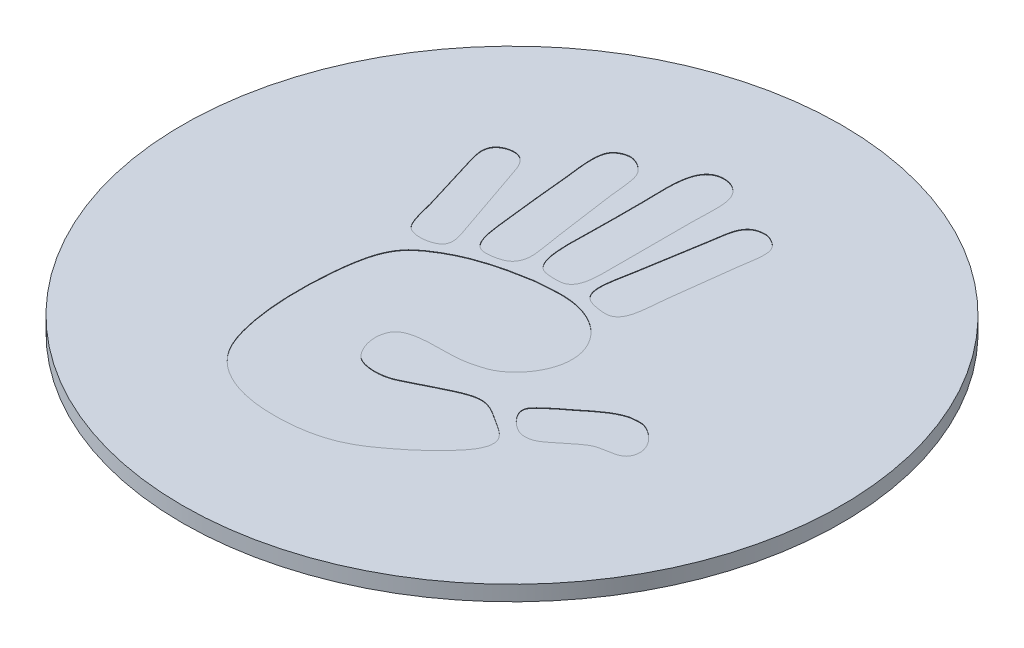
SolidWorks part; units mm, degrees
ref_plane "Front Plane" through (0, 0, 0) normal (0, 0, 1) x (1, 0, 0)
ref_plane "Top Plane" through (0, 0, 0) normal (0, 1, 0) x (1, 0, 0)
ref_plane "Right Plane" through (0, 0, 0) normal (1, 0, 0) x (0, 0, -1)
sketch "Sketch2" plane through (0, 0, 0) normal (0, 1, 0) x (1, 0, 0)
  line L0 (-23.6354, -2.1803) -> (-14.8134, -18.5314)
  line L1 (-14.8134, -18.5314) -> (-14.0145, -18.1003)
  line L2 (22.4832, 1.5913) -> (23.6354, 2.213)
  line L3 (23.6354, 2.213) -> (14.8311, 18.5314)
  line L4 (14.8311, 18.5314) -> (13.9151, 18.0372)
  arc A0 (-9.0807, -18.0316) -> (-14.0145, -18.1003) centre (-11.4817, -22.7946) ccw
  arc A1 (-9.0807, -18.0316) -> (20.1042, -1.9833) centre (0.0088, 0) ccw
  arc A2 (22.4832, 1.5913) -> (20.1042, -1.9833) centre (24.6541, -2.4324) ccw
  arc A3 (9.1926, 17.9838) -> (13.9151, 18.0372) centre (11.503, 22.508) ccw
  arc A4 (9.1926, 17.9838) -> (-20.1066, 1.7689) centre (0.0088, 0) ccw
  ellipse E0 centre (-32.3362, 6.0706) end of major axis (8.5219, 28.1148) minor radius 11.43 (-23.6354, -2.1803) -> (-22.0132, -1.2522) ccw
  spline S0 degree 3 poles (-20.1066, 1.7689) (-20.1338, 1.4588) (-20.1972, 1.1538) (-20.3941, 0.5658) (-20.5253, 0.2882) (-20.7711, -0.1034) (-20.8619, -0.2306) (-21.057, -0.4712) (-21.1612, -0.585) (-21.4939, -0.9069) (-21.7437, -1.0962) (-22.0132, -1.2522) knots 0 0 0 0 0.25 0.25 0.5 0.5 0.625 0.625 0.75 0.75 1 1 1 1
extrude "Boss-Extrude1" add sketch "Sketch2" along normal blind 0.762
sketch "Sketch3" plane through (0, 0.762, 0) normal (0, 1, 0) x (1, 0, 0)
  spline S0 degree 3 poles (-1.1282, 2.7342) (-1.8691, 3.0923) (-1.6328, 5.0692) (-1.6328, 6.1571) (-1.6328, 6.9066) (-1.6328, 7.5655) (-1.6328, 8.1319) (-1.6328, 9.3443) (-1.8554, 11.0728) (-0.7552, 11.2257) knots 5 5 5 5 6 6 6 7 7 7 8 8 8 8
  spline S1 degree 3 poles (-0.053, 2.6903) (-0.229, 2.6221) (-0.8719, 2.6103) (-1.1282, 2.7342) knots 4 4 4 4 5 5 5 5
  spline S2 degree 3 poles (0.4077, 10.5016) (0.5656, 10.0125) (0.4736, 9.223) (0.4736, 8.461) (0.4736, 7.07) (0.4736, 5.6932) (0.4736, 4.2482) (0.4736, 3.4538) (0.3961, 2.8645) (-0.053, 2.6903) knots 1 1 1 1 2 2 2 3 3 3 4 4 4 4
  spline S3 degree 3 poles (-0.7552, 11.2257) (-0.2196, 11.3) (0.2501, 10.99) (0.4077, 10.5016) knots 0 0 0 0 1 1 1 1
  spline S4 degree 3 poles (1.7462, 8.2196) (1.8785, 9.0626) (1.8991, 9.833) (2.7994, 9.8653) knots 7 7 7 7 8 8 8 8
  spline S5 degree 3 poles (1.1977, 4.9064) (1.3429, 5.8845) (1.5932, 7.2455) (1.7462, 8.2196) knots 6 6 6 6 7 7 7 7
  spline S6 degree 3 poles (1.3074, 2.6245) (0.7186, 3.0259) (1.0791, 4.1085) (1.1977, 4.9064) knots 5 5 5 5 6 6 6 6
  spline S7 degree 3 poles (2.4703, 2.427) (2.2313, 2.3604) (1.567, 2.4475) (1.3074, 2.6245) knots 4 4 4 4 5 5 5 5
  spline S8 degree 3 poles (3.1724, 4.5553) (3.0722, 3.7942) (3.1347, 2.6121) (2.4703, 2.427) knots 3 3 3 3 4 4 4 4
  spline S9 degree 3 poles (3.5674, 7.715) (3.441, 6.6447) (3.3126, 5.6204) (3.1724, 4.5553) knots 2 2 2 2 3 3 3 3
  spline S10 degree 3 poles (3.6551, 9.3167) (3.8064, 8.9128) (3.6305, 8.2498) (3.5674, 7.715) knots 1 1 1 1 2 2 2 2
  spline S11 degree 3 poles (2.7994, 9.8653) (3.0754, 9.8752) (3.5326, 9.6439) (3.6551, 9.3167) knots 0 0 0 0 1 1 1 1
  spline S12 degree 3 poles (-4.6169, 9.4703) (-4.4887, 9.681) (-4.2271, 9.8127) (-3.9806, 9.8433) knots 9 9 9 9 10 10 10 10
  spline S13 degree 3 poles (-4.6389, 7.4078) (-4.6837, 7.8997) (-4.9009, 9.0037) (-4.6169, 9.4703) knots 8 8 8 8 9 9 9 9
  spline S14 degree 3 poles (-4.222, 3.5241) (-4.3769, 4.8172) (-4.5206, 6.1106) (-4.6389, 7.4078) knots 7 7 7 7 8 8 8 8
  spline S15 degree 3 poles (-3.5198, 2.054) (-3.9874, 2.1488) (-4.1348, 2.7966) (-4.222, 3.5241) knots 6 6 6 6 7 7 7 7
  spline S16 degree 3 poles (-2.4447, 2.2514) (-2.6908, 2.0945) (-3.2317, 1.9955) (-3.5198, 2.054) knots 5 5 5 5 6 6 6 6
  spline S17 degree 3 poles (-2.0717, 3.2608) (-2.0334, 2.7464) (-2.1681, 2.4279) (-2.4447, 2.2514) knots 4 4 4 4 5 5 5 5
  spline S18 degree 3 poles (-2.2911, 4.7089) (-2.2318, 4.2203) (-2.1058, 3.7197) (-2.0717, 3.2608) knots 3 3 3 3 4 4 4 4
  spline S19 degree 3 poles (-2.708, 7.6711) (-2.5762, 6.7374) (-2.4088, 5.6781) (-2.2911, 4.7089) knots 2 2 2 2 3 3 3 3
  spline S20 degree 3 poles (-2.9274, 9.1412) (-2.7836, 8.7431) (-2.7721, 8.1254) (-2.708, 7.6711) knots 1 1 1 1 2 2 2 2
  spline S21 degree 3 poles (-3.9806, 9.8433) (-3.604, 9.8902) (-3.0714, 9.5397) (-2.9274, 9.1412) knots 0 0 0 0 1 1 1 1
  spline S22 degree 3 poles (-7.8424, 6.6618) (-7.7338, 6.9558) (-7.4296, 7.1155) (-7.1183, 7.1445) knots 7 7 7 7 8 8 8 8
  spline S23 degree 3 poles (-7.6449, 5.3233) (-7.7743, 5.7642) (-7.9833, 6.2802) (-7.8424, 6.6618) knots 6 6 6 6 7 7 7 7
  spline S24 degree 3 poles (-6.8769, 2.8) (-7.1115, 3.6067) (-7.3842, 4.4353) (-7.6449, 5.3233) knots 5 5 5 5 6 6 6 6
  spline S25 degree 3 poles (-6.2845, 1.2421) (-6.6209, 1.5236) (-6.7319, 2.3011) (-6.8769, 2.8) knots 4 4 4 4 5 5 5 5
  spline S26 degree 3 poles (-4.7486, 1.4396) (-4.9781, 1.051) (-5.9312, 0.9465) (-6.2845, 1.2421) knots 3 3 3 3 4 4 4 4
  spline S27 degree 3 poles (-4.7925, 2.2734) (-4.6988, 2.0073) (-4.6208, 1.656) (-4.7486, 1.4396) knots 2 2 2 2 3 3 3 3
  spline S28 degree 3 poles (-6.0212, 5.8499) (-5.5882, 4.5893) (-5.2231, 3.4967) (-4.7925, 2.2734) knots 1 1 1 1 2 2 2 2
  spline S29 degree 3 poles (-7.1183, 7.1445) (-6.3685, 7.2142) (-6.2026, 6.378) (-6.0212, 5.8499) knots 0 0 0 0 1 1 1 1
  spline S30 degree 3 poles (-0.9526, 2.054) (-0.6589, 2.1008) (-0.3704, 2.0916) (-0.053, 2.1198) knots 19 19 19 19 20 20 20 20
  spline S31 degree 3 poles (-4.4853, 0.9349) (-3.4767, 1.523) (-2.3419, 1.8327) (-0.9526, 2.054) knots 18 18 18 18 19 19 19 19
  spline S32 degree 3 poles (-5.5385, 0.1231) (-5.2793, 0.4341) (-4.8654, 0.7133) (-4.4853, 0.9349) knots 17 17 17 17 18 18 18 18
  spline S33 degree 3 poles (-6.3503, -2.5977) (-6.2452, -1.4933) (-6.0872, -0.5353) (-5.5385, 0.1231) knots 16 16 16 16 17 17 17 17
  spline S34 degree 3 poles (-5.736, -8.2806) (-6.3878, -6.9135) (-6.5412, -4.6031) (-6.3503, -2.5977) knots 15 15 15 15 16 16 16 16
  spline S35 degree 3 poles (-3.2565, -10.1237) (-4.3956, -9.8398) (-5.2824, -9.2318) (-5.736, -8.2806) knots 14 14 14 14 15 15 15 15
  spline S36 degree 3 poles (0.6052, -10.014) (-0.609, -10.3752) (-2.1621, -10.3965) (-3.2565, -10.1237) knots 13 13 13 13 14 14 14 14
  spline S37 degree 3 poles (3.3041, -8.3903) (2.4642, -9.0707) (1.7022, -9.6877) (0.6052, -10.014) knots 12 12 12 12 13 13 13 13
  spline S38 degree 3 poles (4.4012, -7.3371) (4.0062, -7.7674) (3.6976, -8.0715) (3.3041, -8.3903) knots 11 11 11 11 12 12 12 12
  spline S39 degree 3 poles (5.1033, -5.9109) (5.1971, -6.4361) (4.6917, -7.0206) (4.4012, -7.3371) knots 10 10 10 10 11 11 11 11
  spline S40 degree 3 poles (4.2037, -5.0113) (4.5637, -5.2444) (5.0302, -5.5017) (5.1033, -5.9109) knots 9 9 9 9 10 10 10 10
  spline S41 degree 3 poles (2.9749, -4.4408) (3.4311, -4.4667) (3.8131, -4.7584) (4.2037, -5.0113) knots 8 8 8 8 9 9 9 9
  spline S42 degree 3 poles (1.2415, -5.0332) (1.7438, -4.8021) (2.426, -4.4096) (2.9749, -4.4408) knots 7 7 7 7 8 8 8 8
  spline S43 degree 3 poles (-0.3383, -5.7792) (0.0666, -5.6579) (0.6458, -5.3074) (1.2415, -5.0332) knots 6 6 6 6 7 7 7 7
  spline S44 degree 3 poles (-1.8303, -5.6915) (-1.4448, -5.9058) (-0.813, -5.9215) (-0.3383, -5.7792) knots 5 5 5 5 6 6 6 6
  spline S45 degree 3 poles (-2.3569, -3.8923) (-2.639, -4.5973) (-2.222, -5.4737) (-1.8303, -5.6915) knots 4 4 4 4 5 5 5 5
  spline S46 degree 3 poles (1.0221, -3.1462) (-0.0727, -3.4118) (-1.9845, -2.9614) (-2.3569, -3.8923) knots 3 3 3 3 4 4 4 4
  spline S47 degree 3 poles (1.9217, -2.861) (1.668, -2.9888) (1.3595, -3.0644) (1.0221, -3.1462) knots 2 2 2 2 3 3 3 3
  spline S48 degree 3 poles (3.2602, 0.4522) (3.8474, -0.9459) (2.8718, -2.3826) (1.9217, -2.861) knots 1 1 1 1 2 2 2 2
  spline S49 degree 3 poles (-0.053, 2.1198) (1.5494, 2.2621) (2.8008, 1.546) (3.2602, 0.4522) knots 0 0 0 0 1 1 1 1
  spline S50 degree 3 poles (7.3633, -1.4787) (7.4269, -1.4613) (7.4808, -1.4669) (7.5608, -1.4567) knots 9 9 9 9 10 10 10 10
  spline S51 degree 3 poles (5.7177, -2.5099) (6.2197, -2.0983) (6.741, -1.6482) (7.3633, -1.4787) knots 8 8 8 8 9 9 9 9
  spline S52 degree 3 poles (4.9716, -3.1023) (5.217, -2.8771) (5.5051, -2.6842) (5.7177, -2.5099) knots 7 7 7 7 8 8 8 8
  spline S53 degree 3 poles (4.3792, -3.8484) (4.3841, -3.5626) (4.6846, -3.3658) (4.9716, -3.1023) knots 6 6 6 6 7 7 7 7
  spline S54 degree 3 poles (5.3885, -4.9235) (4.9957, -4.8403) (4.3719, -4.2718) (4.3792, -3.8484) knots 5 5 5 5 6 6 6 6
  spline S55 degree 3 poles (6.7709, -4.3311) (6.3624, -4.6332) (6.0227, -5.0578) (5.3885, -4.9235) knots 4 4 4 4 5 5 5 5
  spline S56 degree 3 poles (7.7144, -3.6509) (7.3893, -3.7984) (7.0606, -4.1168) (6.7709, -4.3311) knots 3 3 3 3 4 4 4 4
  spline S57 degree 3 poles (9.0748, -3.1462) (8.8596, -3.5448) (8.1193, -3.4671) (7.7144, -3.6509) knots 2 2 2 2 3 3 3 3
  spline S58 degree 3 poles (8.0435, -1.4567) (8.5718, -1.5848) (9.4765, -2.402) (9.0748, -3.1462) knots 1 1 1 1 2 2 2 2
  spline S59 degree 3 poles (7.5608, -1.4567) (7.6413, -1.4465) (7.861, -1.4124) (8.0435, -1.4567) knots 0 0 0 0 1 1 1 1
extrude "Cut-Extrude1" cut sketch "Sketch3" against normal through all
sketch "Sketch5" plane through (0, 0.762, 0) normal (0, 1, 0) x (1, 0, 0)
  line L1 (-29.848, 33.7391) -> (37.109, 33.7391)
  line L2 (-29.848, 33.7391) -> (-29.848, -32.9665)
  line L3 (-29.848, -32.9665) -> (37.109, -32.9665)
  line L4 (37.109, 33.7391) -> (37.109, -32.9665)
  circle A0 centre (0.0088, 0) radius 20.193 construction
  circle A1 centre (0.0088, 0) radius 16.51
  dimension "D1" = 33.02
extrude "Cut-Extrude2" cut sketch "Sketch5" against normal through all
sketch "Sketch7" plane through (0, 0.762, 0) normal (0, 1, 0) x (1, 0, 0)
  circle A2 centre (0.0088, 0) radius 16.51
  circle A3 centre (0.0088, 0) radius 16.51
  dimension "D1" = 0
extrude "Boss-Extrude3" add sketch "Sketch7" against normal offset from surface (0.7366 mm away) 0.0254 up to face at (-0.3822, 0, -6.7879)
sketch "Sketch9" plane through (0, 0.762, 0) normal (0, 1, 0) x (1, 0, 0)
  spline S16 degree 3 poles (-3095.764, -2526.2399) (3123.3369, 2562.8139) (-3137.3899, -2533.6941) (3146.6231, 2473.272) knots -8.557527 -8.557527 -8.557527 -8.557527 19.035336 19.035336 19.035336 19.035336 only from (1.1977, 4.9064) to (1.3074, 2.6245)
  spline S17 degree 3 poles (-1016.7765, -3859.7939) (1035.8712, 3952.7013) (-1035.3417, -3938.9025) (1026.935, 3870.8828) knots -10.71349 -10.71349 -10.71349 -10.71349 23.715667 23.715667 23.715667 23.715667 only from (1.7462, 8.2196) to (1.1977, 4.9064)
  spline S18 degree 3 poles (3295.5782, -2260.9631) (-3314.7192, 2281.6665) (3348.36, -2219.0011) (-3382.3927, 2139.6319) knots -7.025242 -7.025242 -7.025242 -7.025242 22.935092 22.935092 22.935092 22.935092 only from (2.7994, 9.8653) to (1.7462, 8.2196)
  spline S19 degree 3 poles (-3898.3126, 884.962) (3893.2425, -1014.2368) (-3849.031, 1168.6789) (3791.5327, -1270.3118) knots -19.012311 -19.012311 -19.012311 -19.012311 20.118792 20.118792 20.118792 20.118792 only from (3.6551, 9.3167) to (2.7994, 9.8653)
  spline S20 degree 3 poles (3003.7237, 2652.8791) (-3013.6529, -2668.401) (3031.1782, 2672.8873) (-3027.1825, -2600.7338) knots -17.720569 -17.720569 -17.720569 -17.720569 20.297542 20.297542 20.297542 20.297542 only from (3.5674, 7.715) to (3.6551, 9.3167)
  spline S21 degree 3 poles (-471.1883, -3966.9869) (441.5568, 3832.8889) (-417.0462, -3822.7841) (424.5912, 3985.2122) knots -32.960104 -32.960104 -32.960104 -32.960104 37.918216 37.918216 37.918216 37.918216 only from (3.1724, 4.5553) to (3.5674, 7.715)
  spline S22 degree 3 poles (-2179.0397, 3354.8429) (2155.2022, -3411.1409) (-2123.0133, 3435.5851) (2107.3587, -3397.0534) knots -9.664312 -9.664312 -9.664312 -9.664312 17.136069 17.136069 17.136069 17.136069 only from (2.4703, 2.427) to (3.1724, 4.5553)
  spline S23 degree 3 poles (3995.8195, -198.2506) (-4017.7675, 277.0857) (4016.2829, -340.9695) (-3976.4498, 409.4185) knots -12.428208 -12.428208 -12.428208 -12.428208 21.381402 21.381402 21.381402 21.381402 only from (1.3074, 2.6245) to (2.4703, 2.427)
  spline S24 degree 3 poles (1.1977, 4.9064) (1.0791, 4.1085) (0.7186, 3.0259) (1.3074, 2.6245) knots 5 5 5 5 6 6 6 6
  spline S25 degree 3 poles (1.7462, 8.2196) (1.5932, 7.2455) (1.3429, 5.8845) (1.1977, 4.9064) knots 6 6 6 6 7 7 7 7
  spline S26 degree 3 poles (2.7994, 9.8653) (1.8991, 9.833) (1.8785, 9.0626) (1.7462, 8.2196) knots 7 7 7 7 8 8 8 8
  spline S27 degree 3 poles (3.6551, 9.3167) (3.5326, 9.6439) (3.0754, 9.8752) (2.7994, 9.8653) knots 0 0 0 0 1 1 1 1
  spline S28 degree 3 poles (3.5674, 7.715) (3.6305, 8.2498) (3.8064, 8.9128) (3.6551, 9.3167) knots 1 1 1 1 2 2 2 2
  spline S29 degree 3 poles (3.1724, 4.5553) (3.3126, 5.6204) (3.441, 6.6447) (3.5674, 7.715) knots 2 2 2 2 3 3 3 3
  spline S30 degree 3 poles (2.4703, 2.427) (3.1347, 2.6121) (3.0722, 3.7942) (3.1724, 4.5553) knots 3 3 3 3 4 4 4 4
  spline S31 degree 3 poles (1.3074, 2.6245) (1.567, 2.4475) (2.2313, 2.3604) (2.4703, 2.427) knots 4 4 4 4 5 5 5 5
  spline S32 degree 3 poles (-3175.8378, 2434.3295) (-36.4904, 67.3954) (0.4736, -13.1033) (0.4736, 4.2482) (0.4736, 5.6932) (0.4736, 7.07) (0.4736, 8.461) (0.4736, 24.1547) (39.5081, 51.547) (-2869.5101, -2775.5992) knots -19.842069 -19.842069 -19.842069 -19.842069 2 2 2 3 3 3 23.596173 23.596173 23.596173 23.596173 only from (-0.053, 2.6903) to (0.4077, 10.5016)
  spline S33 degree 3 poles (3972.5737, 458.22) (-4007.8398, -396.4799) (4011.7989, 346.3165) (-3989.3096, -286.5983) knots -12.275486 -12.275486 -12.275486 -12.275486 21.202959 21.202959 21.202959 21.202959 only from (-1.1282, 2.7342) to (-0.053, 2.6903)
  spline S34 degree 3 poles (2436.5507, -3160.0671) (-32.5536, 108.4317) (-1.6328, 22.4233) (-1.6328, 8.1319) (-1.6328, 7.5655) (-1.6328, 6.9066) (-1.6328, 6.1571) (-1.6328, -6.5094) (-33.6617, -139.6907) (1817.5783, 3564.7777) knots -5.787592 -5.787592 -5.787592 -5.787592 6 6 6 7 7 7 18.643178 18.643178 18.643178 18.643178 only from (-0.7552, 11.2257) to (-1.1282, 2.7342)
  spline S35 degree 3 poles (-3382.9717, 2135.2595) (3184.6086, -2420.1101) (-2952.2242, 2719.3511) (2686.5942, -2945.1574) knots -22.773491 -22.773491 -22.773491 -22.773491 23.550804 23.550804 23.550804 23.550804 only from (0.4077, 10.5016) to (-0.7552, 11.2257)
  spline S36 degree 3 poles (-0.053, 2.6903) (0.3961, 2.8645) (0.4736, 3.4538) (0.4736, 4.2482) (0.4736, 5.6932) (0.4736, 7.07) (0.4736, 8.461) (0.4736, 9.223) (0.5656, 10.0125) (0.4077, 10.5016) knots 1 1 1 1 2 2 2 3 3 3 4 4 4 4
  spline S37 degree 3 poles (-1.1282, 2.7342) (-0.8719, 2.6103) (-0.229, 2.6221) (-0.053, 2.6903) knots 4 4 4 4 5 5 5 5
  spline S38 degree 3 poles (-0.7552, 11.2257) (-1.8554, 11.0728) (-1.6328, 9.3443) (-1.6328, 8.1319) (-1.6328, 7.5655) (-1.6328, 6.9066) (-1.6328, 6.1571) (-1.6328, 5.0692) (-1.8691, 3.0923) (-1.1282, 2.7342) knots 5 5 5 5 6 6 6 7 7 7 8 8 8 8
  spline S39 degree 3 poles (0.4077, 10.5016) (0.2501, 10.99) (-0.2196, 11.3) (-0.7552, 11.2257) knots 0 0 0 0 1 1 1 1
  spline S56 degree 3 poles (3827.6525, 1135.0392) (-3871.1576, -816.4124) (3856.8167, 835.4945) (-3815.5815, -1186.8377) knots -55.966256 -55.966256 -55.966256 -55.966256 73.431662 73.431662 73.431662 73.431662 only from (-4.6389, 7.4078) to (-4.222, 3.5241)
  spline S57 degree 3 poles (1977.2357, -3464.7223) (-1941.6752, 3552.5708) (1883.3645, -3562.5842) (-1840.2246, 3561.15) knots -5.595375 -5.595375 -5.595375 -5.595375 22.721906 22.721906 22.721906 22.721906 only from (-4.6169, 9.4703) to (-4.6389, 7.4078)
  spline S58 degree 3 poles (-3913.3808, -831.1765) (3959.9311, 686.2838) (-3993.4882, -493.8088) (3981.036, 332.26) knots -20.702281 -20.702281 -20.702281 -20.702281 39.096568 39.096568 39.096568 39.096568 only from (-3.9806, 9.8433) to (-4.6169, 9.4703)
  spline S59 degree 3 poles (-3499.6444, 1949.2057) (3430.2664, -2092.6878) (-3345.6841, 2254.2554) (3219.2873, -2356.8577) knots -17.912337 -17.912337 -17.912337 -17.912337 18.843591 18.843591 18.843591 18.843591 only from (-2.9274, 9.1412) to (-3.9806, 9.8433)
  spline S60 degree 3 poles (1724.1373, 3615.5728) (-1744.3122, -3633.9872) (1757.7666, 3641.1516) (-1786.6717, -3570.9141) knots -19.760193 -19.760193 -19.760193 -19.760193 22.558671 22.558671 22.558671 22.558671 only from (-2.708, 7.6711) to (-2.9274, 9.1412)
  spline S61 degree 3 poles (-1516.3629, 3706.7271) (1510.0822, -3805.8224) (-1498.6079, 3824.3616) (1462.195, -3714.1649) knots -23.546646 -23.546646 -23.546646 -23.546646 28.426834 28.426834 28.426834 28.426834 only from (-2.2911, 4.7089) to (-2.708, 7.6711)
  spline S62 degree 3 poles (-3796.6164, 1267.9633) (3807.4648, -1300.3085) (-3817.0278, 1292.6119) (3807.7226, -1211.921) knots -25.260779 -25.260779 -25.260779 -25.260779 32.459145 32.459145 32.459145 32.459145 only from (-2.0717, 3.2608) to (-2.2911, 4.7089)
  spline S63 degree 3 poles (1684.9837, -3620.1859) (-1989.6705, 3573.8882) (2122.2532, -3484.8728) (-2148.6775, 3378.0896) knots -39.439829 -39.439829 -39.439829 -39.439829 41.201324 41.201324 41.201324 41.201324 only from (-2.4447, 2.2514) to (-2.0717, 3.2608)
  spline S64 degree 3 poles (3907.7355, 837.7287) (-3959.5817, -758.6069) (3968.3, 682.0826) (-3957.6475, -591.5849) knots -13.834269 -13.834269 -13.834269 -13.834269 24.829077 24.829077 24.829077 24.829077 only from (-3.5198, 2.054) to (-2.4447, 2.2514)
  spline S65 degree 3 poles (-1936.2727, -3498.7736) (1931.3677, 3558.6844) (-1949.2937, -3544.9252) (1955.9246, 3488.9566) knots -13.737129 -13.737129 -13.737129 -13.737129 25.367565 25.367565 25.367565 25.367565 only from (-4.222, 3.5241) to (-3.5198, 2.054)
  spline S66 degree 3 poles (-4.6389, 7.4078) (-4.5206, 6.1106) (-4.3769, 4.8172) (-4.222, 3.5241) knots 7 7 7 7 8 8 8 8
  spline S67 degree 3 poles (-4.6169, 9.4703) (-4.9009, 9.0037) (-4.6837, 7.8997) (-4.6389, 7.4078) knots 8 8 8 8 9 9 9 9
  spline S68 degree 3 poles (-3.9806, 9.8433) (-4.2271, 9.8127) (-4.4887, 9.681) (-4.6169, 9.4703) knots 9 9 9 9 10 10 10 10
  spline S69 degree 3 poles (-2.9274, 9.1412) (-3.0714, 9.5397) (-3.604, 9.8902) (-3.9806, 9.8433) knots 0 0 0 0 1 1 1 1
  spline S70 degree 3 poles (-2.708, 7.6711) (-2.7721, 8.1254) (-2.7836, 8.7431) (-2.9274, 9.1412) knots 1 1 1 1 2 2 2 2
  spline S71 degree 3 poles (-2.2911, 4.7089) (-2.4088, 5.6781) (-2.5762, 6.7374) (-2.708, 7.6711) knots 2 2 2 2 3 3 3 3
  spline S72 degree 3 poles (-2.0717, 3.2608) (-2.1058, 3.7197) (-2.2318, 4.2203) (-2.2911, 4.7089) knots 3 3 3 3 4 4 4 4
  spline S73 degree 3 poles (-2.4447, 2.2514) (-2.1681, 2.4279) (-2.0334, 2.7464) (-2.0717, 3.2608) knots 4 4 4 4 5 5 5 5
  spline S74 degree 3 poles (-3.5198, 2.054) (-3.2317, 1.9955) (-2.6908, 2.0945) (-2.4447, 2.2514) knots 5 5 5 5 6 6 6 6
  spline S75 degree 3 poles (-4.222, 3.5241) (-4.1348, 2.7966) (-3.9874, 2.1488) (-3.5198, 2.054) knots 6 6 6 6 7 7 7 7
  spline S82 degree 3 poles (3013.787, 2622.1984) (-3147.5515, -2384.3751) (3213.061, 2291.0263) (-3266.8481, -2314.6818) knots -34.0885 -34.0885 -34.0885 -34.0885 45.568972 45.568972 45.568972 45.568972 only from (-7.6449, 5.3233) to (-6.8769, 2.8)
  spline S83 degree 3 poles (3612.8173, -1692.9166) (-3628.3953, 1766.2394) (3601.3377, -1779.3604) (-3593.5352, 1777.2391) knots -13.555681 -13.555681 -13.555681 -13.555681 27.120073 27.120073 27.120073 27.120073 only from (-7.8424, 6.6618) to (-7.6449, 5.3233)
  spline S84 degree 3 poles (-3999.2381, -217.3164) (4015.5257, 32.7299) (-4025.5663, 182.1603) (3972.7996, -370.171) knots -20.762782 -20.762782 -20.762782 -20.762782 34.659546 34.659546 34.659546 34.659546 only from (-7.1183, 7.1445) to (-7.8424, 6.6618)
  spline S85 degree 3 poles (1714.1461, 3616.8704) (-1760.0638, -3616.4555) (1792.9824, 3606.1701) (-1862.0065, -3536.3391) knots -14.162413 -14.162413 -14.162413 -14.162413 14.57936 14.57936 14.57936 14.57936 only from (-6.0212, 5.8499) to (-7.1183, 7.1445)
  spline S86 degree 3 poles (1629.1816, -3648.5686) (-1597.22, 3552.4859) (1580.3732, -3547.6661) (-1621.3815, 3665.0063) knots -21.429944 -21.429944 -21.429944 -21.429944 24.323918 24.323918 24.323918 24.323918 only from (-4.7925, 2.2734) to (-6.0212, 5.8499)
  spline S87 degree 3 poles (-2713.0087, 2944.4774) (2652.6818, -3019.2018) (-2603.5191, 3074.5499) (2527.5748, -3093.5764) knots -21.183347 -21.183347 -21.183347 -21.183347 26.812935 26.812935 26.812935 26.812935 only from (-4.7486, 1.4396) to (-4.7925, 2.2734)
  spline S88 degree 3 poles (3952.7793, 565.9869) (-4012.5515, -422.9183) (4014.1348, 280.7553) (-4001.6494, -130.8624) knots -10.987779 -10.987779 -10.987779 -10.987779 17.939713 17.939713 17.939713 17.939713 only from (-6.2845, 1.2421) to (-4.7486, 1.4396)
  spline S89 degree 3 poles (-1247.2967, -3799.8382) (1254.2815, 3834.4356) (-1298.5039, -3819.3565) (1326.1047, 3772.4579) knots -12.680408 -12.680408 -12.680408 -12.680408 21.352423 21.352423 21.352423 21.352423 only from (-6.8769, 2.8) to (-6.2845, 1.2421)
  spline S90 degree 3 poles (-7.6449, 5.3233) (-7.3842, 4.4353) (-7.1115, 3.6067) (-6.8769, 2.8) knots 5 5 5 5 6 6 6 6
  spline S91 degree 3 poles (-7.8424, 6.6618) (-7.9833, 6.2802) (-7.7743, 5.7642) (-7.6449, 5.3233) knots 6 6 6 6 7 7 7 7
  spline S92 degree 3 poles (-7.1183, 7.1445) (-7.4296, 7.1155) (-7.7338, 6.9558) (-7.8424, 6.6618) knots 7 7 7 7 8 8 8 8
  spline S93 degree 3 poles (-6.0212, 5.8499) (-6.2026, 6.378) (-6.3685, 7.2142) (-7.1183, 7.1445) knots 0 0 0 0 1 1 1 1
  spline S94 degree 3 poles (-4.7925, 2.2734) (-5.2231, 3.4967) (-5.5882, 4.5893) (-6.0212, 5.8499) knots 1 1 1 1 2 2 2 2
  spline S95 degree 3 poles (-4.7486, 1.4396) (-4.6208, 1.656) (-4.6988, 2.0073) (-4.7925, 2.2734) knots 2 2 2 2 3 3 3 3
  spline S96 degree 3 poles (-6.2845, 1.2421) (-5.9312, 0.9465) (-4.9781, 1.051) (-4.7486, 1.4396) knots 3 3 3 3 4 4 4 4
  spline S97 degree 3 poles (-6.8769, 2.8) (-6.7319, 2.3011) (-6.6209, 1.5236) (-6.2845, 1.2421) knots 4 4 4 4 5 5 5 5
  spline S130 degree 3 poles (-3951.8588, -643.6622) (3995.3707, 592.6744) (-4015.0978, -511.4127) (3973.1756, 406.1526) knots -10.456339 -10.456339 -10.456339 -10.456339 44.885938 44.885938 44.885938 44.885938 only from (-4.4853, 0.9349) to (-5.5385, 0.1231)
  spline S131 degree 3 poles (2693.4209, 2949.583) (-2289.9667, -3114.1817) (2004.676, 3316.7743) (-1855.461, -3542.9467) knots -7.374638 -7.374638 -7.374638 -7.374638 44.028989 44.028989 44.028989 44.028989 only from (-0.9526, 2.054) to (-4.4853, 0.9349)
  spline S132 degree 3 poles (1453.3245, 3728.339) (-1382.0933, -3734.134) (1349.8155, 3750.1641) (-1360.2587, -3759.6631) knots -14.786784 -14.786784 -14.786784 -14.786784 53.695539 53.695539 53.695539 53.695539 only from (-0.053, 2.1198) to (-0.9526, 2.054)
  spline S133 degree 3 poles (-3242.5853, 2320.3674) (2907.1543, -2746.2517) (-2488.6206, 3125.0399) (2006.1411, -3444.5244) knots -17.863176 -17.863176 -17.863176 -17.863176 18.638457 18.638457 18.638457 18.638457 only from (3.2602, 0.4522) to (-0.053, 2.1198)
  spline S134 degree 3 poles (3167.5107, 2438.5868) (-3345.4267, -2265.9039) (3490.8375, 2035.8041) (-3582.1942, -1766.3083) knots -11.615799 -11.615799 -11.615799 -11.615799 14.17794 14.17794 14.17794 14.17794 only from (1.9217, -2.861) to (3.2602, 0.4522)
  spline S135 degree 3 poles (1466.3234, -3723.8839) (-1602.5454, 3668.2793) (1688.0772, -3638.6039) (-1715.4749, 3609.51) knots -37.824081 -37.824081 -37.824081 -37.824081 41.644355 41.644355 41.644355 41.644355 only from (1.0221, -3.1462) to (1.9217, -2.861)
  spline S136 degree 3 poles (2964.3974, -2686.4354) (-3026.1985, 2677.6029) (3026.9681, -2682.6951) (-2969.1288, 2675.7) knots -7.196512 -7.196512 -7.196512 -7.196512 14.508045 14.508045 14.508045 14.508045 only from (-2.3569, -3.8923) to (1.0221, -3.1462)
  spline S137 degree 3 poles (-2410.5316, 3186.0665) (2569.2142, -3106.7039) (-2721.2272, 2967.1142) (2848.0126, -2807.6601) knots -10.927538 -10.927538 -10.927538 -10.927538 19.856086 19.856086 19.856086 19.856086 only from (-1.8303, -5.6915) to (-2.3569, -3.8923)
  spline S138 degree 3 poles (-3995.9129, -169.2948) (4023.9409, 318.9609) (-4009.4427, -489.6836) (3945.4536, 634.5149) knots -16.148797 -16.148797 -16.148797 -16.148797 26.840613 26.840613 26.840613 26.840613 only from (-0.3383, -5.7792) to (-1.8303, -5.6915)
  spline S139 degree 3 poles (-1741.3215, -3604.9629) (1842.0627, 3597.6623) (-1885.8975, -3584.5888) (1880.2685, 3524.279) knots -16.551023 -16.551023 -16.551023 -16.551023 28.901961 28.901961 28.901961 28.901961 only from (1.2415, -5.0332) to (-0.3383, -5.7792)
  spline S140 degree 3 poles (-1794.5939, -3577.3094) (1889.7476, 3562.2158) (-1934.7328, -3546.2505) (1943.9994, 3491.3061) knots -10.580218 -10.580218 -10.580218 -10.580218 25.897628 25.897628 25.897628 25.897628 only from (2.9749, -4.4408) to (1.2415, -5.0332)
  spline S141 degree 3 poles (1077.9608, 3848.0295) (-1035.4513, -3881.2519) (1045.5525, 3870.7424) (-1075.8058, -3855.8222) knots -15.212192 -15.212192 -15.212192 -15.212192 31.462453 31.462453 31.462453 31.462453 only from (4.2037, -5.0113) to (2.9749, -4.4408)
  spline S142 degree 3 poles (-3850.1796, -1071.1914) (3899.3269, 1003.5427) (-3900.5022, -976.035) (3889.019, 947.5012) knots -10.008017 -10.008017 -10.008017 -10.008017 29.632907 29.632907 29.632907 29.632907 only from (5.1033, -5.9109) to (4.2037, -5.0113)
  spline S143 degree 3 poles (3666.757, 1600.1722) (-3714.2134, -1558.2025) (3757.873, 1457.8723) (-3759.815, -1354.6548) knots -6.269169 -6.269169 -6.269169 -6.269169 26.949279 26.949279 26.949279 26.949279 only from (4.4012, -7.3371) to (5.1033, -5.9109)
  spline S144 degree 3 poles (-3141.3221, -2480.2338) (3074.6238, 2475.1874) (-3030.3851, -2536.3855) (3038.055, 2599.2986) knots -14.799334 -14.799334 -14.799334 -14.799334 37.476291 37.476291 37.476291 37.476291 only from (3.3041, -8.3903) to (4.4012, -7.3371)
  spline S145 degree 3 poles (-3475.1488, 1969.4044) (3449.2097, -1972.4122) (-3478.4379, 1886.8011) (3587.5606, -1781.0723) knots -7.435578 -7.435578 -7.435578 -7.435578 33.26523 33.26523 33.26523 33.26523 only from (0.6052, -10.014) to (3.3041, -8.3903)
  spline S146 degree 3 poles (3995.1337, 37.2265) (-4079.6511, 126.3486) (4066.1776, -335.6197) (-3964.0053, 508.1945) knots -3.635872 -3.635872 -3.635872 -3.635872 30.738642 30.738642 30.738642 30.738642 only from (-3.2565, -10.1237) to (0.6052, -10.014)
  spline S147 degree 3 poles (3843.0923, 1058.5511) (-4050.8505, -687.1777) (4104.2949, 202.8062) (-3977.7589, 321.222) knots -11.581046 -11.581046 -11.581046 -11.581046 44.692524 44.692524 44.692524 44.692524 only from (-5.736, -8.2806) to (-3.2565, -10.1237)
  spline S148 degree 3 poles (-257.7599, -3993.7372) (412.1647, 4087.1828) (-589.6745, -4073.0132) (738.906, 3920.3889) knots 0.401744 0.401744 0.401744 0.401744 30.007043 30.007043 30.007043 30.007043 only from (-6.3503, -2.5977) to (-5.736, -8.2806)
  spline S149 degree 3 poles (3598.2698, -1735.0934) (-3645.099, 1731.4688) (3675.2631, -1638.0617) (-3740.2474, 1426.2309) knots -4.846705 -4.846705 -4.846705 -4.846705 39.420108 39.420108 39.420108 39.420108 only from (-5.5385, 0.1231) to (-6.3503, -2.5977)
  spline S150 degree 3 poles (-4.4853, 0.9349) (-4.8654, 0.7133) (-5.2793, 0.4341) (-5.5385, 0.1231) knots 17 17 17 17 18 18 18 18
  spline S151 degree 3 poles (-0.9526, 2.054) (-2.3419, 1.8327) (-3.4767, 1.523) (-4.4853, 0.9349) knots 18 18 18 18 19 19 19 19
  spline S152 degree 3 poles (-0.053, 2.1198) (-0.3704, 2.0916) (-0.6589, 2.1008) (-0.9526, 2.054) knots 19 19 19 19 20 20 20 20
  spline S153 degree 3 poles (3.2602, 0.4522) (2.8008, 1.546) (1.5494, 2.2621) (-0.053, 2.1198) knots 0 0 0 0 1 1 1 1
  spline S154 degree 3 poles (1.9217, -2.861) (2.8718, -2.3826) (3.8474, -0.9459) (3.2602, 0.4522) knots 1 1 1 1 2 2 2 2
  spline S155 degree 3 poles (1.0221, -3.1462) (1.3595, -3.0644) (1.668, -2.9888) (1.9217, -2.861) knots 2 2 2 2 3 3 3 3
  spline S156 degree 3 poles (-2.3569, -3.8923) (-1.9845, -2.9614) (-0.0727, -3.4118) (1.0221, -3.1462) knots 3 3 3 3 4 4 4 4
  spline S157 degree 3 poles (-1.8303, -5.6915) (-2.222, -5.4737) (-2.639, -4.5973) (-2.3569, -3.8923) knots 4 4 4 4 5 5 5 5
  spline S158 degree 3 poles (-0.3383, -5.7792) (-0.813, -5.9215) (-1.4448, -5.9058) (-1.8303, -5.6915) knots 5 5 5 5 6 6 6 6
  spline S159 degree 3 poles (1.2415, -5.0332) (0.6458, -5.3074) (0.0666, -5.6579) (-0.3383, -5.7792) knots 6 6 6 6 7 7 7 7
  spline S160 degree 3 poles (2.9749, -4.4408) (2.426, -4.4096) (1.7438, -4.8021) (1.2415, -5.0332) knots 7 7 7 7 8 8 8 8
  spline S161 degree 3 poles (4.2037, -5.0113) (3.8131, -4.7584) (3.4311, -4.4667) (2.9749, -4.4408) knots 8 8 8 8 9 9 9 9
  spline S162 degree 3 poles (5.1033, -5.9109) (5.0302, -5.5017) (4.5637, -5.2444) (4.2037, -5.0113) knots 9 9 9 9 10 10 10 10
  spline S163 degree 3 poles (4.4012, -7.3371) (4.6917, -7.0206) (5.1971, -6.4361) (5.1033, -5.9109) knots 10 10 10 10 11 11 11 11
  spline S164 degree 3 poles (3.3041, -8.3903) (3.6976, -8.0715) (4.0062, -7.7674) (4.4012, -7.3371) knots 11 11 11 11 12 12 12 12
  spline S165 degree 3 poles (0.6052, -10.014) (1.7022, -9.6877) (2.4642, -9.0707) (3.3041, -8.3903) knots 12 12 12 12 13 13 13 13
  spline S166 degree 3 poles (-3.2565, -10.1237) (-2.1621, -10.3965) (-0.609, -10.3752) (0.6052, -10.014) knots 13 13 13 13 14 14 14 14
  spline S167 degree 3 poles (-5.736, -8.2806) (-5.2824, -9.2318) (-4.3956, -9.8398) (-3.2565, -10.1237) knots 14 14 14 14 15 15 15 15
  spline S168 degree 3 poles (-6.3503, -2.5977) (-6.5412, -4.6031) (-6.3878, -6.9135) (-5.736, -8.2806) knots 15 15 15 15 16 16 16 16
  spline S169 degree 3 poles (-5.5385, 0.1231) (-6.0872, -0.5353) (-6.2452, -1.4933) (-6.3503, -2.5977) knots 16 16 16 16 17 17 17 17
  spline S170 degree 3 poles (-3974.1151, 396.5942) (4011.4269, -432.6003) (-3993.9407, 483.3342) (3963.8214, -571.6217) knots -24.719136 -24.719136 -24.719136 -24.719136 39.940685 39.940685 39.940685 39.940685 only from (5.7177, -2.5099) to (4.9716, -3.1023)
  spline S171 degree 3 poles (1082.3844, -3853.8033) (-995.2253, 3895.3124) (978.1755, -3908.0572) (-984.3221, 3872.9208) knots -14.121939 -14.121939 -14.121939 -14.121939 31.928328 31.928328 31.928328 31.928328 only from (7.3633, -1.4787) to (5.7177, -2.5099)
  spline S172 degree 3 poles (2762.0359, 2898.6515) (-2714.3944, -2921.4581) (2707.0423, 2939.1855) (-2680.4173, -2963.5595) knots -32.792434 -32.792434 -32.792434 -32.792434 51.90526 51.90526 51.90526 51.90526 only from (7.5608, -1.4567) to (7.3633, -1.4787)
  spline S173 degree 3 poles (-3393.514, -2105.2011) (3465.4386, 2040.19) (-3485.7964, -1981.1206) (3517.3494, 1916.5161) knots -26.652727 -26.652727 -26.652727 -26.652727 27.354633 27.354633 27.354633 27.354633 only from (8.0435, -1.4567) to (7.5608, -1.4567)
  spline S174 degree 3 poles (-3728.1897, 1419.5886) (3711.0541, -1594.2163) (-3628.7459, 1735.3611) (3550.4209, -1857.3788) knots -11.297302 -11.297302 -11.297302 -11.297302 14.619876 14.619876 14.619876 14.619876 only from (9.0748, -3.1462) to (8.0435, -1.4567)
  spline S175 degree 3 poles (3040.7564, -2611.1879) (-3050.8535, 2605.511) (3061.3623, -2619.4712) (-3006.159, 2624.9435) knots -12.870409 -12.870409 -12.870409 -12.870409 17.619703 17.619703 17.619703 17.619703 only from (7.7144, -3.6509) to (9.0748, -3.1462)
  spline S176 degree 3 poles (639.4528, 3945.2122) (-629.295, -3981.9229) (617.0747, 3977.7215) (-545.7875, -3964.9988) knots -20.969694 -20.969694 -20.969694 -20.969694 27.750567 27.750567 27.750567 27.750567 only from (6.7709, -4.3311) to (7.7144, -3.6509)
  spline S177 degree 3 poles (-1895.3714, 3514.3719) (1882.6347, -3544.8657) (-1871.0676, 3534.9024) (1913.0878, -3520.5167) knots -12.490513 -12.490513 -12.490513 -12.490513 22.126071 22.126071 22.126071 22.126071 only from (5.3885, -4.9235) to (6.7709, -4.3311)
  spline S178 degree 3 poles (3340.2887, -2209.7439) (-3284.4802, 2324.7029) (3221.2336, -2433.7686) (-3112.1006, 2500.2802) knots -10.000569 -10.000569 -10.000569 -10.000569 21.115588 21.115588 21.115588 21.115588 only from (4.3792, -3.8484) to (5.3885, -4.9235)
  spline S179 degree 3 poles (-3517.484, 1891.269) (3578.0807, -1826.3252) (-3593.3599, 1771.1714) (3602.2496, -1751.3803) knots -16.502934 -16.502934 -16.502934 -16.502934 28.748217 28.748217 28.748217 28.748217 only from (4.9716, -3.1023) to (4.3792, -3.8484)
  spline S180 degree 3 poles (5.7177, -2.5099) (5.5051, -2.6842) (5.217, -2.8771) (4.9716, -3.1023) knots 7 7 7 7 8 8 8 8
  spline S181 degree 3 poles (7.3633, -1.4787) (6.741, -1.6482) (6.2197, -2.0983) (5.7177, -2.5099) knots 8 8 8 8 9 9 9 9
  spline S182 degree 3 poles (7.5608, -1.4567) (7.4808, -1.4669) (7.4269, -1.4613) (7.3633, -1.4787) knots 9 9 9 9 10 10 10 10
  spline S183 degree 3 poles (8.0435, -1.4567) (7.861, -1.4124) (7.6413, -1.4465) (7.5608, -1.4567) knots 0 0 0 0 1 1 1 1
  spline S184 degree 3 poles (9.0748, -3.1462) (9.4765, -2.402) (8.5718, -1.5848) (8.0435, -1.4567) knots 1 1 1 1 2 2 2 2
  spline S185 degree 3 poles (7.7144, -3.6509) (8.1193, -3.4671) (8.8596, -3.5448) (9.0748, -3.1462) knots 2 2 2 2 3 3 3 3
  spline S186 degree 3 poles (6.7709, -4.3311) (7.0606, -4.1168) (7.3893, -3.7984) (7.7144, -3.6509) knots 3 3 3 3 4 4 4 4
  spline S187 degree 3 poles (5.3885, -4.9235) (6.0227, -5.0578) (6.3624, -4.6332) (6.7709, -4.3311) knots 4 4 4 4 5 5 5 5
  spline S188 degree 3 poles (4.3792, -3.8484) (4.3719, -4.2718) (4.9957, -4.8403) (5.3885, -4.9235) knots 5 5 5 5 6 6 6 6
  spline S189 degree 3 poles (4.9716, -3.1023) (4.6846, -3.3658) (4.3841, -3.5626) (4.3792, -3.8484) knots 6 6 6 6 7 7 7 7
  dimension "D1" = 0
  dimension "D2" = 0
  dimension "D3" = 0
  dimension "D4" = 0
  dimension "D5" = 0
  dimension "D6" = 0
extrude "Cut-Extrude3" cut sketch "Sketch9" against normal blind 0.0254
